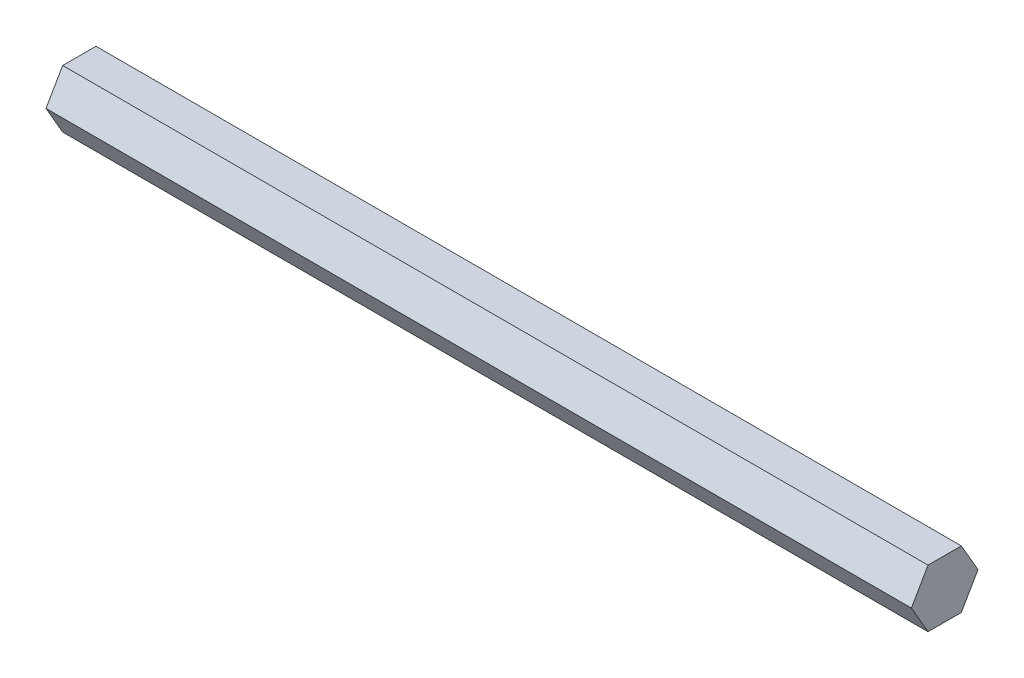
SolidWorks part; units mm, degrees
ref_plane "Front Plane" through (0, 0, 0) normal (0, 0, 1) x (1, 0, 0)
ref_plane "Top Plane" through (0, 0, 0) normal (0, 1, 0) x (1, 0, 0)
ref_plane "Right Plane" through (0, 0, 0) normal (1, 0, 0) x (0, 0, -1)
sketch "Sketch1" plane through (0, 0, 0) normal (1, 0, 0) x (0, 0, -1)
  line L0 (0, 6.35) -> (0, 0)
  line L1 (7.3323, 0) -> (3.6662, 6.35)
  line L2 (3.6662, 6.35) -> (-3.6662, 6.35)
  line L3 (-3.6662, 6.35) -> (-7.3323, 0)
  line L4 (-7.3323, 0) -> (-3.6662, -6.35)
  line L5 (-3.6662, -6.35) -> (3.6662, -6.35)
  line L6 (3.6662, -6.35) -> (7.3323, 0)
  circle A0 centre (0, 0) radius 6.35 construction
extrude "Boss-Extrude1" add sketch "Sketch1" along normal blind 190.5
